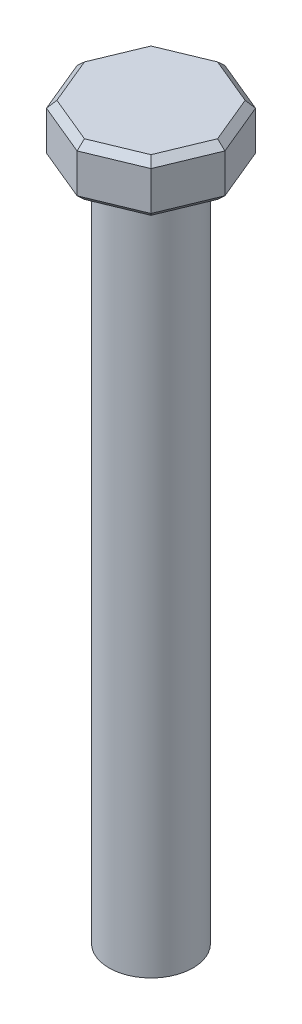
SolidWorks part; units mm, degrees
ref_plane "Front Plane" through (0, 0, 0) normal (0, 0, 1) x (1, 0, 0)
ref_plane "Top Plane" through (0, 0, 0) normal (0, 1, 0) x (1, 0, 0)
ref_plane "Right Plane" through (0, 0, 0) normal (1, 0, 0) x (0, 0, -1)
sketch "Sketch1" plane through (0, 0, 0) normal (0, 1, 0) x (1, 0, 0)
  circle A0 centre (0, 0) radius 4
  dimension "D1" = 8
extrude "Boss-Extrude1" add sketch "Sketch1" along normal blind 64.5
cosmetic thread "Cosmetic Thread1" parameters "D1"=7.4, "D2"=6.619
sketch "Sketch2" plane through (0, 64.5, 0) normal (0, 1, 0) x (1, 0, 0)
  line L1 (7.0355, 0) -> (4.9749, 4.9749)
  line L2 (4.9749, 4.9749) -> (0, 7.0355)
  line L3 (0, 7.0355) -> (-4.9749, 4.9749)
  line L4 (-4.9749, 4.9749) -> (-7.0355, 0)
  line L5 (-7.0355, 0) -> (-4.9749, -4.9749)
  line L6 (-4.9749, -4.9749) -> (0, -7.0355)
  line L7 (0, -7.0355) -> (4.9749, -4.9749)
  line L8 (4.9749, -4.9749) -> (7.0355, 0)
  circle A0 centre (0, 0) radius 6.5 construction
  dimension "D1" = 13
extrude "Boss-Extrude2" add sketch "Sketch2" along normal blind 5
chamfer "Chamfer1" distance 0.65 angle 45 16 edges at (2.4874, 69.5, 6.0052) (-2.4874, 69.5, 6.0052) (-6.0052, 69.5, 2.4874) (-6.0052, 69.5, -2.4874) (-2.4874, 69.5, -6.0052) (2.4874, 69.5, -6.0052) (6.0052, 69.5, -2.4874) (6.0052, 69.5, 2.4874) (-6.0052, 64.5, -2.4874) (-2.4874, 64.5, -6.0052) (2.4874, 64.5, -6.0052) (6.0052, 64.5, -2.4874) (6.0052, 64.5, 2.4874) (2.4874, 64.5, 6.0052) (-2.4874, 64.5, 6.0052) (-6.0052, 64.5, 2.4874)
